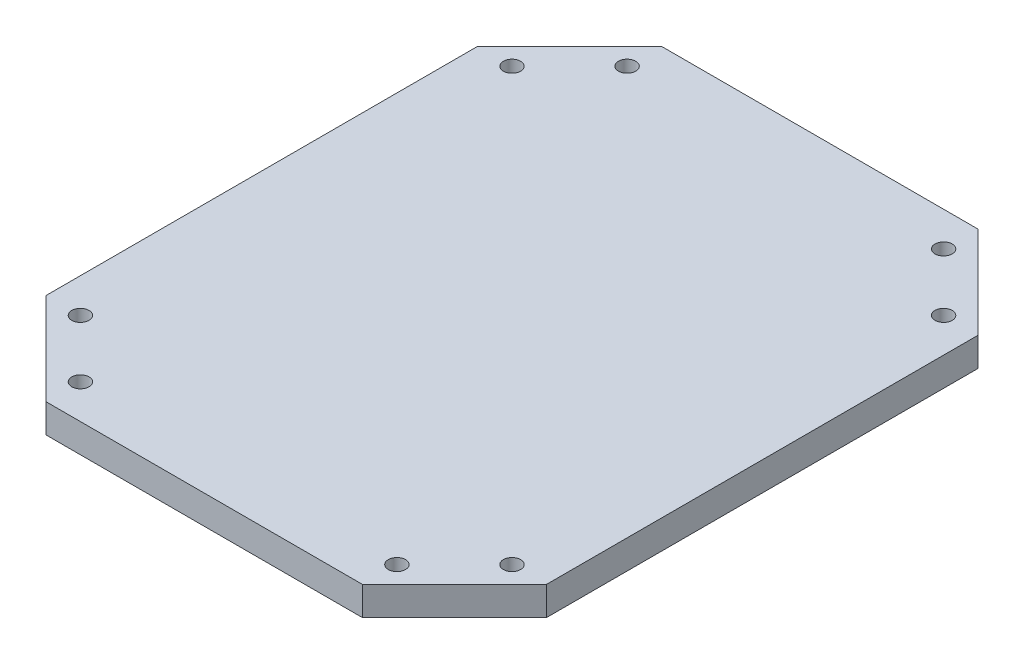
SolidWorks part; units mm, degrees
ref_plane "Front Plane" through (0, 0, 0) normal (0, 0, 1) x (1, 0, 0)
ref_plane "Top Plane" through (0, 0, 0) normal (0, 1, 0) x (1, 0, 0)
ref_plane "Right Plane" through (0, 0, 0) normal (1, 0, 0) x (0, 0, -1)
sketch "Sketch1" plane through (0, 0, 0) normal (0, 1, 0) x (1, 0, 0)
  line L0 (-36.8332, 10.919) -> (-20.8533, 26.8988)
  line L1 (-20.8533, 26.8988) -> (34.1467, 26.8988)
  line L2 (34.1467, 26.8988) -> (50.1265, 10.919)
  line L3 (50.1265, 10.919) -> (50.1265, -64.081)
  line L4 (50.1265, -64.081) -> (34.1467, -80.0609)
  line L5 (34.1467, -80.0609) -> (-20.8533, -80.0609)
  line L6 (-20.8533, -80.0609) -> (-36.8332, -64.081)
  line L7 (-36.8332, -64.081) -> (-36.8332, 10.919)
  dimension "D1" = 55
  dimension "D2" = 75
extrude "Boss-Extrude1" add sketch "Sketch1" along normal blind 5
sketch "Sketch4" plane through (0, 5, 0) normal (0, 1, 0) x (1, 0, 0)
  line L0 (-20.8533, 26.8988) -> (-20.8533, -80.0609) construction
  line L1 (-36.8332, 10.919) -> (50.1265, 10.919) construction
  line L2 (34.1467, 26.8988) -> (34.1467, -80.0609) construction
  line L3 (34.1467, 26.8988) -> (-20.8533, 26.8988) construction
  line L4 (-36.8332, -64.081) -> (50.1265, -64.081) construction
hole_wizard "Ø3.0 (3) Diameter Hole2" positions "3DSketch3" profile "Sketch5" hole size "Ø3.0" standard "AS" end condition up to next
sketch3d "3DSketch3"
  line L0 (-36.8332, 5, -10.919) -> (50.1265, 5, -10.919) construction
  line L1 (-20.8533, 5, -26.8988) -> (-20.8533, 5, 80.0609) construction
  point P0 (-30.8533, 5, -10.919)
  point P4 (-20.8533, 5, -20.919)
  dimension "D1" = 10
  dimension "D2" = 10
sketch "Sketch5" plane through (-30.8533, 5, -10.919) normal (1, 0, 0) x (0, 0, 1)
  line L0 (0, 0) -> (0, 5)
  line L1 (0, 5) -> (1.5, 5)
  line L2 (1.5, 5) -> (1.5, 0)
  line L5 (1.5, 0) -> (0, 0)
  line L11 (0, -6.35) -> (0, 107.95) construction
  dimension "Thru Hole Dia." = 3
  dimension "Thru Hole Depth" = 5
hole_wizard "Ø3.0 (3) Diameter Hole3" positions "3DSketch4" profile "Sketch6" hole size "Ø3.0" standard "AS" end condition up to next
sketch3d "3DSketch4"
  line L0 (34.1467, 5, -26.8988) -> (34.1467, 5, 80.0609) construction
  line L1 (-36.8332, 5, -10.919) -> (50.1265, 5, -10.919) construction
  point P0 (34.1467, 5, -20.919)
  point P4 (44.1467, 5, -10.919)
  dimension "D1" = 10
  dimension "D2" = 10
sketch "Sketch6" plane through (34.1467, 5, -20.919) normal (1, 0, 0) x (0, 0, 1)
  line L0 (0, 0) -> (0, 5)
  line L1 (0, 5) -> (1.5, 5)
  line L2 (1.5, 5) -> (1.5, 0)
  line L5 (1.5, 0) -> (0, 0)
  line L11 (0, -6.35) -> (0, 107.95) construction
  dimension "Thru Hole Dia." = 3
  dimension "Thru Hole Depth" = 5
hole_wizard "Ø3.0 (3) Diameter Hole4" positions "3DSketch5" profile "Sketch7" hole size "Ø3.0" standard "AS" end condition up to next
sketch3d "3DSketch5"
  line L0 (-36.8332, 5, 64.081) -> (50.1265, 5, 64.081) construction
  line L1 (-20.8533, 5, -26.8988) -> (-20.8533, 5, 80.0609) construction
  line L2 (34.1467, 5, -26.8988) -> (34.1467, 5, 80.0609) construction
  point P0 (-30.8533, 5, 64.081)
  point P4 (-20.8533, 5, 74.081)
  point P8 (34.1467, 5, 74.081)
  point P12 (44.1467, 5, 64.081)
  dimension "D1" = 10
  dimension "D2" = 10
  dimension "D3" = 10
  dimension "D4" = 10
sketch "Sketch7" plane through (-30.8533, 5, 64.081) normal (1, 0, 0) x (0, 0, 1)
  line L0 (0, 0) -> (0, 5)
  line L1 (0, 5) -> (1.5, 5)
  line L2 (1.5, 5) -> (1.5, 0)
  line L5 (1.5, 0) -> (0, 0)
  line L11 (0, -6.35) -> (0, 107.95) construction
  dimension "Thru Hole Dia." = 3
  dimension "Thru Hole Depth" = 5
